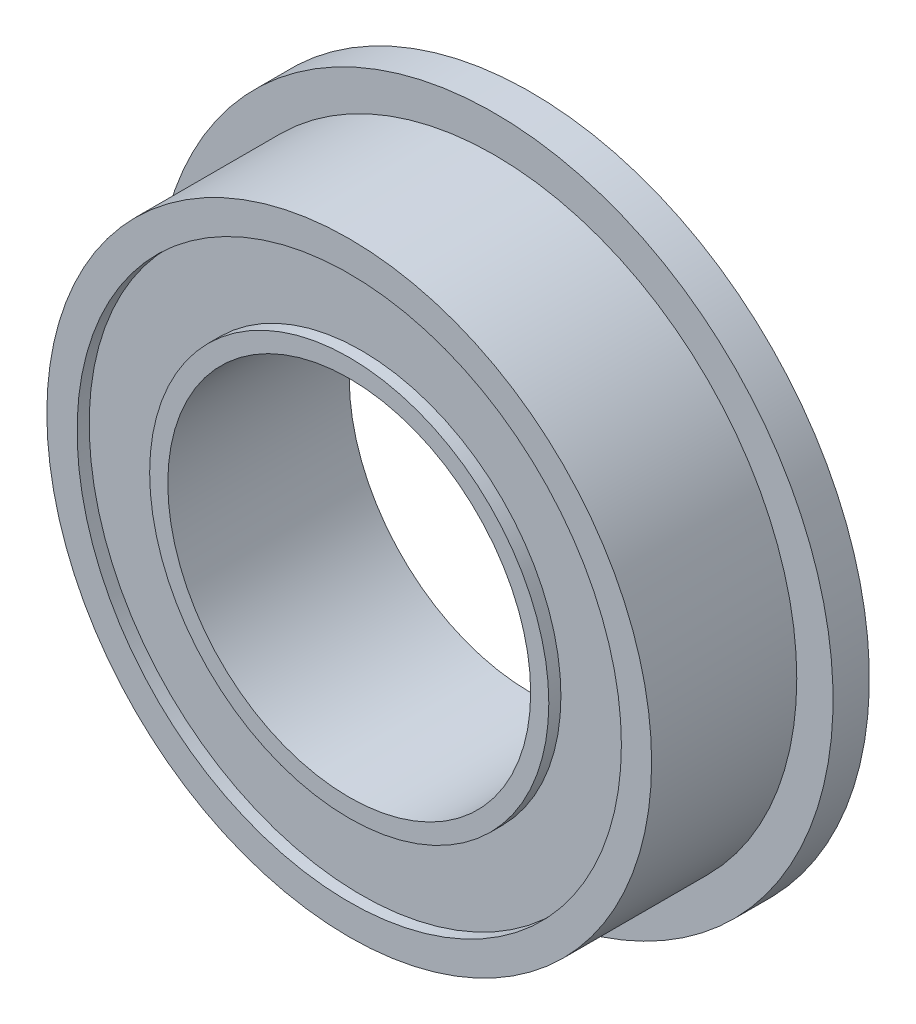
SolidWorks part; units mm, degrees
material "鉻不鏽鋼"
ref_plane "前基準面" through (0, 0, 0) normal (0, 0, 1) x (1, 0, 0)
ref_plane "上基準面" through (0, 0, 0) normal (0, 1, 0) x (1, 0, 0)
ref_plane "右基準面" through (0, 0, 0) normal (1, 0, 0) x (0, 0, -1)
sketch "草圖1" plane through (0, 0, 0) normal (0, 0, 1) x (1, 0, 0)
  circle A0 centre (0, 0) radius 5
  dimension "D1" = 10
extrude "填料-伸長1" add sketch "草圖1" along normal mid plane 3
sketch "草圖4" plane through (0, 0, -1.5) normal (0, 0, -1) x (-1, 0, 0)
  circle A0 centre (0, 0) radius 5.6
  dimension "D1" = 11.2
extrude "填料-伸長2" add sketch "草圖4" against normal blind 0.6
sketch "草圖2" plane through (0, 0, 1.5) normal (0, 0, 1) x (1, 0, 0)
  circle A0 centre (0, 0) radius 3
  dimension "D1" = 6
extrude "除料-伸長1" cut sketch "草圖2" against normal through all
sketch "草圖3" plane through (0, 0, 1.5) normal (0, 0, 1) x (1, 0, 0)
  circle A0 centre (0, 0) radius 4.5
  circle A1 centre (0, 0) radius 3.3
  dimension "D1" = 6.6
  dimension "D2" = 9
extrude "除料-伸長2" cut sketch "草圖3" against normal blind 0.2
mirror "鏡射1" about plane through (0, 0, 0) normal (0, 0, 1) of "除料-伸長2"
